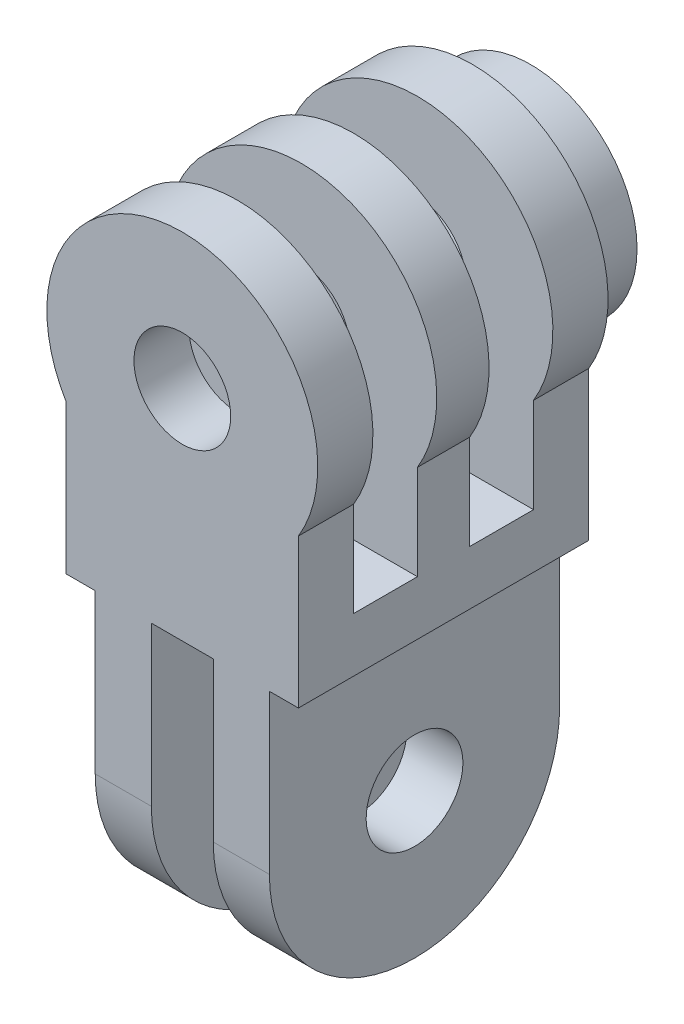
SolidWorks part; units mm, degrees
ref_plane "Plan de face" through (0, 0, 0) normal (0, 0, 1) x (1, 0, 0)
ref_plane "Plan de dessus" through (0, 0, 0) normal (0, 1, 0) x (1, 0, 0)
ref_plane "Plan de droite" through (0, 0, 0) normal (1, 0, 0) x (0, 0, -1)
sketch "Esquisse1" plane through (0, 0, 0) normal (0, 0, 1) x (1, 0, 0)
  line L1 (-6, -17) -> (6, -17)
  line L2 (-6, -17) -> (-6, 17)
  line L3 (-6, 17) -> (6, 17)
  line L4 (6, -17) -> (6, 17)
  line L5 (-6, -17) -> (6, 17) construction
  line L6 (-6, 17) -> (6, -17) construction
  line L7 (6, -1.3026) -> (4.5, -1.3026)
  line L8 (6, -1.3026) -> (6, -17)
  line L9 (6, -17) -> (4.5, -17)
  line L10 (4.5, -1.3026) -> (4.5, -17)
  line L11 (-6, -1.3026) -> (-4.5, -1.3026)
  line L12 (-6, -1.3026) -> (-6, -17)
  line L13 (-6, -17) -> (-4.5, -17)
  line L14 (-4.5, -1.3026) -> (-4.5, -17)
  line L15 (1.6, -17) -> (-1.6, -17)
  line L16 (1.6, -17) -> (1.6, -1.3026)
  line L17 (1.6, -1.3026) -> (-1.6, -1.3026)
  line L18 (-1.6, -17) -> (-1.6, -1.3026)
  circle A0 centre (0, 10) radius 7
  circle A1 centre (0, 10) radius 2.5
  point P0 (0, 0)
  dimension "D4" = 1.5
  dimension "D1" = 7
  dimension "D2" = 34
  dimension "D3" = 12
  dimension "D5" = 3.2
  dimension "D6" = 1.5
  dimension "D7" = 2.9
extrude "Boss.-Extru.1" add sketch "Esquisse1" along normal blind 15 contours A0 L2 L11 L14 L1 L18 L17 L16 L10 L7 L4 | L4 A0 L2 A1 | L4 A0 | L2 A0
sketch "Esquisse2" plane through (4.5, 0, 0) normal (1, 0, 0) x (0, 0, -1)
  line L0 (0, 17) -> (-15, 17) construction
  line L1 (-12.15, 17) -> (-8.85, 17)
  line L2 (-12.15, 17) -> (-12.15, 1.5)
  line L3 (-12.15, 1.5) -> (-8.85, 1.5)
  line L4 (-8.85, 17) -> (-8.85, 1.5)
  line L6 (-6.15, 17) -> (-2.85, 17)
  line L7 (-6.15, 17) -> (-6.15, 1.5)
  line L8 (-6.15, 1.5) -> (-2.85, 1.5)
  line L9 (-2.85, 17) -> (-2.85, 1.5)
  dimension "D1" = 15.5
  dimension "D2" = 3.3
  dimension "D3" = 3.3
  dimension "D4" = 2.85
  dimension "D5" = 2.85
  dimension "D6" = 15.5
extrude "Enlèv. mat.-Extru.1" cut sketch "Esquisse2" against normal through all and the other way through all
sketch "Esquisse5" plane through (4.5, 0, 0) normal (1, 0, 0) x (0, 0, -1)
  line L0 (0, -1.3026) -> (0, -17) construction
  line L2 (-15, -17) -> (0, -17) construction
  line L3 (0, -9.5) -> (0, -17)
  line L4 (0, -17) -> (-7.5, -17)
  line L5 (-7.5, -17) -> (-15, -17)
  line L6 (-15, -17) -> (-15, -9.5)
  circle A0 centre (-7.5, -9.5) radius 7.5
  circle A1 centre (-7.5, -9.5) radius 2.5
  line M1 (0, -17) -> (0, -1.3026)
  line M3 (-15, -1.3026) -> (-15, -17)
  line M4 (-15, -17) -> (0, -17)
  dimension "D1" = 7.5
  dimension "D3" = 5
  dimension "D2" = 7.5
extrude "Enlèv. mat.-Extru.4" cut sketch "Esquisse5" against normal blind 10 contours A0 M3 M4 | A0 M4 M1 | A1
sketch "Esquisse6" plane through (0, 0, 0) normal (0, 0, -1) x (-1, 0, 0)
  circle A0 centre (0, 10) radius 5.5
  circle A1 centre (0, 10) radius 2.5
extrude "Boss.-Extru.2" add sketch "Esquisse6" along normal blind 3
sketch "Esquisse7" plane through (0, 0, -3) normal (0, 0, -1) x (-1, 0, 0)
  line L0 (0, 14.7071) -> (3.8971, 12.4571)
  line L1 (3.8971, 12.4571) -> (3.8971, 7.9571)
  line L2 (3.8971, 7.9571) -> (0, 5.7071)
  line L3 (0, 5.7071) -> (-3.8971, 7.9571)
  line L4 (-3.8971, 7.9571) -> (-3.8971, 12.4571)
  line L5 (-3.8971, 12.4571) -> (0, 14.7071)
  line L6 (0, 10) -> (0, 0) construction
  point P2 (0, 10)
  dimension "D1" = 120
extrude "Enlèv. mat.-Extru.5" cut sketch "Esquisse7" against normal blind 3
